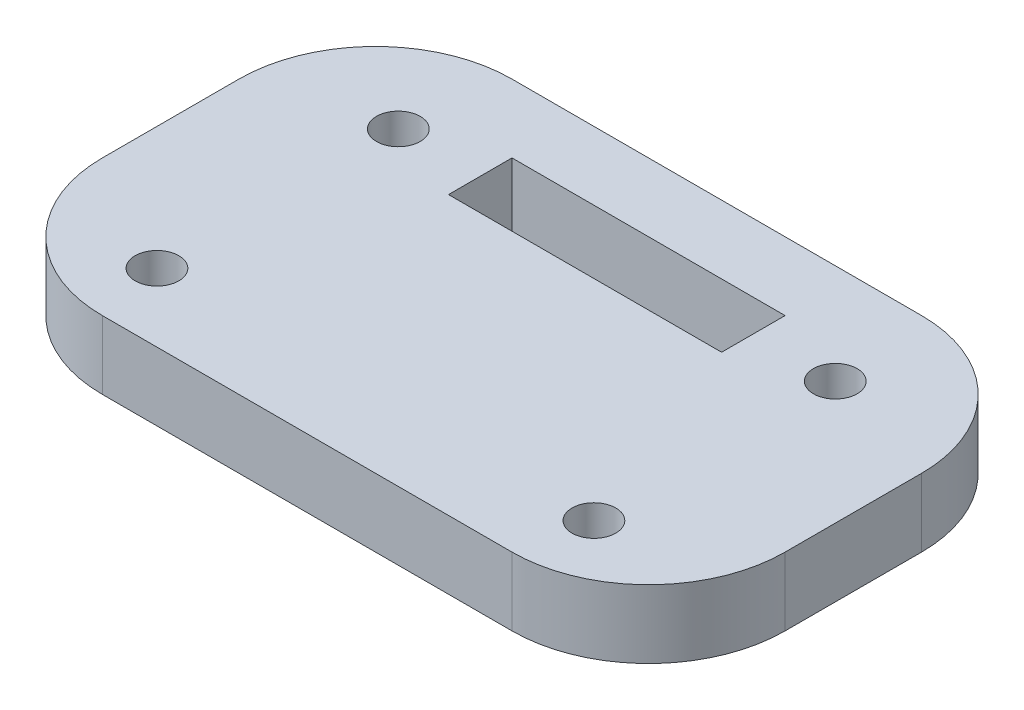
SolidWorks part; units mm, degrees
ref_plane "Front Plane" through (0, 0, 0) normal (0, 0, 1) x (1, 0, 0)
ref_plane "Top Plane" through (0, 0, 0) normal (0, 1, 0) x (1, 0, 0)
ref_plane "Right Plane" through (0, 0, 0) normal (1, 0, 0) x (0, 0, -1)
sketch "Sketch2" plane through (0, 0, 0) normal (0, 1, 0) x (1, 0, 0)
  line L1 (10, 0) -> (40, 0)
  line L2 (0, 10) -> (0, 20)
  line L3 (10, 30) -> (40, 30)
  line L4 (50, 10) -> (50, 20)
  line L5 (15, 25) -> (35, 25)
  line L6 (15, 25) -> (15, 20.35)
  line L7 (15, 20.35) -> (35, 20.35)
  line L8 (35, 25) -> (35, 20.35)
  circle A0 centre (9, 5) radius 1.6
  circle A1 centre (41, 5) radius 1.6
  circle A2 centre (9, 22.675) radius 1.6
  circle A3 centre (41, 22.675) radius 1.6
  arc A4 (10, 0) -> (0, 10) centre (10, 10) cw
  arc A5 (40, 0) -> (50, 10) centre (40, 10) ccw
  arc A6 (40, 30) -> (50, 20) centre (40, 20) cw
  arc A7 (0, 20) -> (10, 30) centre (10, 20) cw
  point P9 (25, 25)
  point P20 (0, 0)
  point P25 (50, 30)
  point P28 (0, 30)
  dimension "D7" = 3.2
  dimension "D11" = 3.2
  dimension "D13" = 3.2
  dimension "D14" = 3.2
  dimension "D18" = 10
  dimension "D1" = 4.65
  dimension "D2" = 20
  dimension "D3" = 50
  dimension "D4" = 5
  dimension "D5" = 15
  dimension "D6" = 30
  dimension "D8" = 9
  dimension "D9" = 5
  dimension "D10" = 5
  dimension "D12" = 32
  dimension "D15" = 32
  dimension "D16" = 9
  dimension "D17" = 7.325
extrude "Boss-Extrude1" add sketch "Sketch2" along normal blind 5
